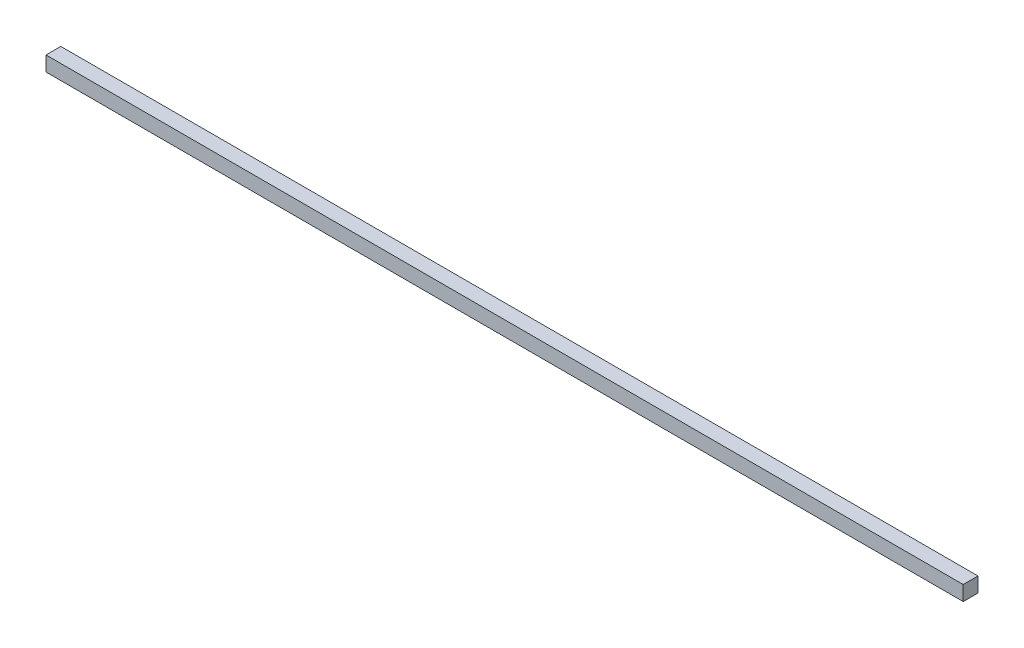
SolidWorks part; units mm, degrees
ref_plane "Front Plane" through (0, 0, 0) normal (0, 0, 1) x (1, 0, 0)
ref_plane "Top Plane" through (0, 0, 0) normal (0, 1, 0) x (1, 0, 0)
ref_plane "Right Plane" through (0, 0, 0) normal (1, 0, 0) x (0, 0, -1)
sketch "Sketch1" plane through (0, 0, 0) normal (0, 1, 0) x (1, 0, 0)
  line L1 (-72.2996, 81.0915) -> (113.7004, 81.0915)
  line L2 (-72.2996, 81.0915) -> (-72.2996, 84.0915)
  line L3 (-72.2996, 84.0915) -> (113.7004, 84.0915)
  line L4 (113.7004, 81.0915) -> (113.7004, 84.0915)
  dimension "D1" = 186
  dimension "D2" = 3
extrude "Boss-Extrude1" add sketch "Sketch1" along normal blind 3
